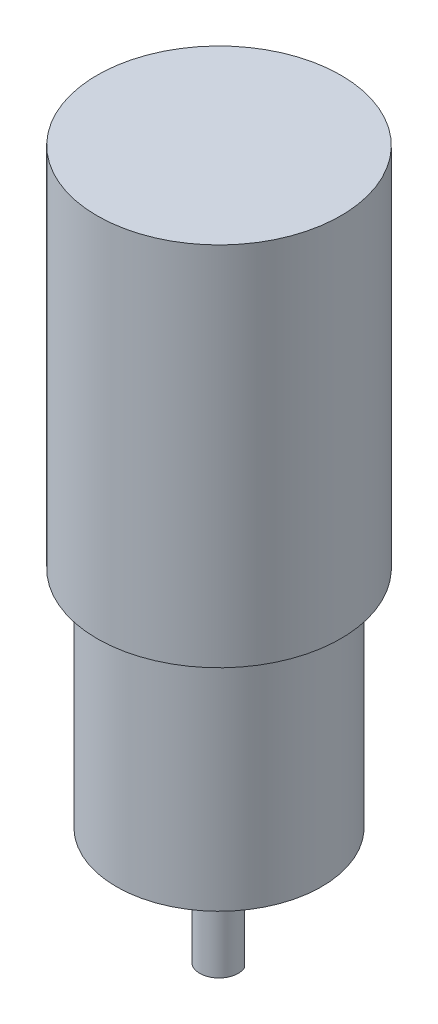
SolidWorks part; units mm, degrees
ref_plane "Front Plane" through (0, 0, 0) normal (0, 0, 1) x (1, 0, 0)
ref_plane "Top Plane" through (0, 0, 0) normal (0, 1, 0) x (1, 0, 0)
ref_plane "Right Plane" through (0, 0, 0) normal (1, 0, 0) x (0, 0, -1)
sketch "Sketch2" plane through (0, 0, 0) normal (0, 1, 0) x (1, 0, 0)
  line L0 (-2.75, 1.199) -> (2.75, 1.199)
  circle A0 centre (0, 0) radius 3
  dimension "D1" = 6
  dimension "D2" = 5.5
extrude "Boss-Extrude1" add sketch "Sketch2" along normal blind 12 contours L0 A0
sketch "Sketch3" plane through (0, 12, 0) normal (0, 1, 0) x (1, 0, 0)
  arc A0 (-2.75, 1.199) -> (2.75, 1.199) centre (0, 0) ccw construction
  arc A1 (-2.75, 1.199) -> (2.75, 1.199) centre (0, 0) ccw
  circle A2 centre (0, 0) radius 3
  line M1 (2.75, 1.199) -> (-2.75, 1.199)
  arc M2 (-2.75, 1.199) -> (2.75, 1.199) centre (0, 0) ccw
extrude "Boss-Extrude2" add sketch "Sketch3" along normal blind 3.2 contours A2 M1 | M2 M1
sketch "Sketch5" plane through (0, 15.2, 0) normal (0, 1, 0) x (1, 0, 0)
  line L0 (-9, 4.3589) -> (-9, -4.3589)
  line L1 (9, 4.3589) -> (9, -4.3589)
  arc A0 (-9, -4.3589) -> (9, -4.3589) centre (0, 0) ccw
  arc A1 (9, 4.3589) -> (-9, 4.3589) centre (0, 0) ccw
  dimension "D1" = 20
  dimension "D2" = 18
extrude "Boss-Extrude3" add sketch "Sketch5" along normal blind 3
sketch "Sketch6" plane through (0, 18.2, 0) normal (0, 1, 0) x (1, 0, 0)
  circle A0 centre (0, 0) radius 16
  dimension "D1" = 32
extrude "Boss-Extrude4" add sketch "Sketch6" along normal blind 35
sketch "Sketch7" plane through (0, 53.2, 0) normal (0, 1, 0) x (1, 0, 0)
  circle A0 centre (0, 0) radius 19
  dimension "D1" = 38
extrude "Boss-Extrude5" add sketch "Sketch7" along normal blind 57.1
